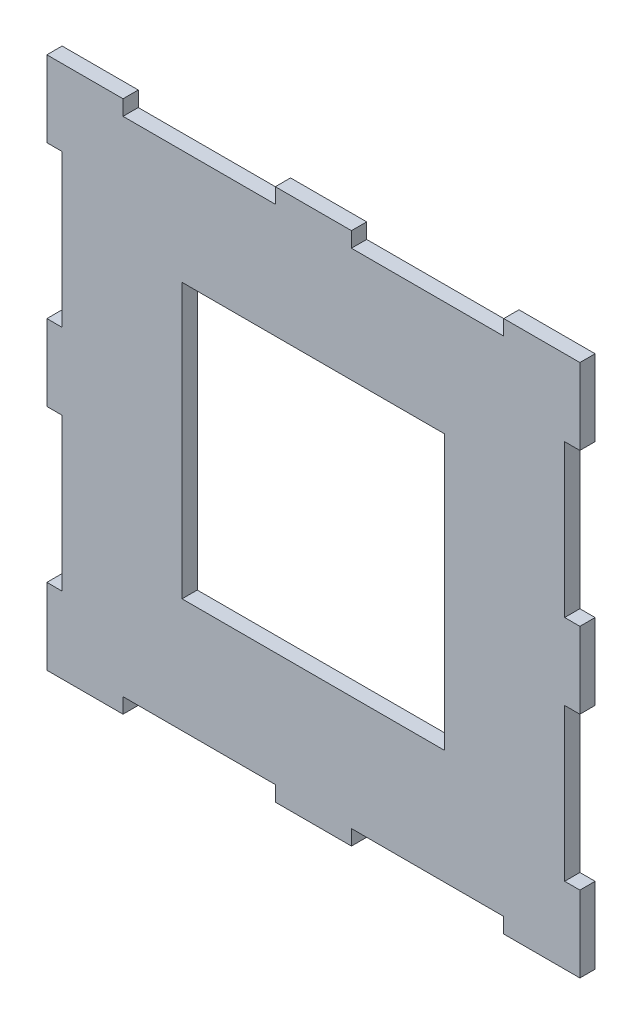
SolidWorks part; units mm, degrees
ref_plane "Front Plane" through (0, 0, 0) normal (0, 0, 1) x (1, 0, 0)
ref_plane "Top Plane" through (0, 0, 0) normal (0, 1, 0) x (1, 0, 0)
ref_plane "Right Plane" through (0, 0, 0) normal (1, 0, 0) x (0, 0, -1)
sketch "Sketch1" plane through (0, 0, 0) normal (0, 0, 1) x (1, 0, 0)
  line L1 (-35, -35) -> (35, -35)
  line L2 (-35, -35) -> (-35, 35)
  line L3 (-35, 35) -> (35, 35)
  line L4 (35, -35) -> (35, 35)
  line L5 (0, 35) -> (0, -35) construction
  line L6 (-35, 0) -> (35, 0) construction
  line L7 (-17.25, -18) -> (17.25, -18)
  line L8 (-17.25, -18) -> (-17.25, 18)
  line L9 (-17.25, 18) -> (17.25, 18)
  line L10 (17.25, -18) -> (17.25, 18)
  line L11 (0, 18) -> (0, -18) construction
  line L12 (-17.25, 0) -> (17.25, 0) construction
  point P0 (0, 0)
  point P4 (0, 0)
  dimension "D1" = 70
  dimension "D2" = 70
  dimension "D3" = 34.5
  dimension "D4" = 36
extrude "Boss-Extrude1" add sketch "Sketch1" against normal blind 2
sketch "Sketch2" plane through (0, 0, 0) normal (0, 0, 1) x (1, 0, 0)
  line L0 (-35, 35) -> (-25, 35)
  line L1 (35, 35) -> (-35, 35) construction
  line L2 (-25, 35) -> (-5, 35)
  line L3 (-5, 35) -> (5, 35)
  line L4 (5, 35) -> (25, 35)
  line L6 (35, 35) -> (35, 25)
  line L7 (-25, 33) -> (-5, 33)
  line L8 (-25, 33) -> (-25, 37)
  line L9 (-25, 37) -> (-5, 37)
  line L10 (-5, 33) -> (-5, 37)
  line L11 (-15, 37) -> (-15, 33) construction
  line L12 (-25, 35) -> (-5, 35) construction
  line L13 (5, 33) -> (25, 33)
  line L14 (5, 33) -> (5, 37)
  line L15 (5, 37) -> (25, 37)
  line L16 (25, 33) -> (25, 37)
  line L17 (15, 37) -> (15, 33) construction
  line L18 (5, 35) -> (25, 35) construction
  line L19 (35, -35) -> (35, 35) construction
  line L20 (35, 25) -> (35, 5)
  line L21 (35, 5) -> (35, -5)
  line L22 (35, -5) -> (35, -25)
  line L23 (-35, -35) -> (-25, -35)
  line L24 (35, -5) -> (33, -5)
  line L25 (35, -5) -> (35, -25)
  line L26 (35, -25) -> (33, -25)
  line L27 (33, -5) -> (33, -25)
  line L28 (35, 25) -> (33, 25)
  line L29 (35, 25) -> (35, 5)
  line L30 (35, 5) -> (33, 5)
  line L31 (33, 25) -> (33, 5)
  line L32 (-35, -35) -> (35, -35) construction
  line L33 (-25, -35) -> (-5, -35)
  line L34 (-5, -35) -> (5, -35)
  line L35 (5, -35) -> (25, -35)
  line L36 (-35, 35) -> (-35, 25)
  line L37 (-25, -35) -> (-5, -35)
  line L38 (-25, -35) -> (-25, -33)
  line L39 (-25, -33) -> (-5, -33)
  line L40 (-5, -35) -> (-5, -33)
  line L41 (5, -35) -> (25, -35)
  line L42 (5, -35) -> (5, -33)
  line L43 (5, -33) -> (25, -33)
  line L44 (25, -35) -> (25, -33)
  line L45 (-35, 35) -> (-35, -35) construction
  line L46 (-35, 25) -> (-35, 5)
  line L47 (-35, 5) -> (-35, -5)
  line L48 (-35, -5) -> (-35, -25)
  line L50 (-35, 25) -> (-33, 25)
  line L51 (-35, 25) -> (-35, 5)
  line L52 (-35, 5) -> (-33, 5)
  line L53 (-33, 25) -> (-33, 5)
  line L54 (-35, -5) -> (-33, -5)
  line L55 (-35, -5) -> (-35, -25)
  line L56 (-35, -25) -> (-33, -25)
  line L57 (-33, -5) -> (-33, -25)
  point P7 (15, 35)
  point P9 (-15, 35)
  point P10 (-15, 35)
  point P14 (15, 35)
  line M25 (35, -35) -> (35, 35)
  line M26 (35, 35) -> (-35, 35)
  line M27 (-35, 35) -> (-35, -35)
  line M28 (-35, -35) -> (35, -35)
  dimension "D1" = 10
  dimension "D2" = 20
  dimension "D3" = 10
  dimension "D4" = 20
  dimension "D5" = 4
  dimension "D6" = 20
  dimension "D7" = 20
  dimension "D8" = 4
  dimension "D9" = 10
  dimension "D10" = 20
  dimension "D11" = 10
  dimension "D12" = 20
  dimension "D13" = 2
  dimension "D14" = 2
  dimension "D15" = 10
  dimension "D16" = 20
  dimension "D17" = 10
  dimension "D18" = 20
  dimension "D19" = 20
  dimension "D20" = 20
  dimension "D21" = 2
  dimension "D22" = 2
  dimension "D23" = 10
  dimension "D24" = 20
  dimension "D25" = 10
  dimension "D26" = 20
  dimension "D27" = 2
  dimension "D28" = 2
extrude "Cut-Extrude1" cut sketch "Sketch2" against normal blind 2 contours L53 L50 L52 M27 | L57 L54 L56 M27 | L40 L39 L38 M28 | L44 L43 L42 M28 | L24 L27 L26 M25 | L28 L31 L30 M25 | L13 L16 L14 M26 | L7 L10 L8 M26
